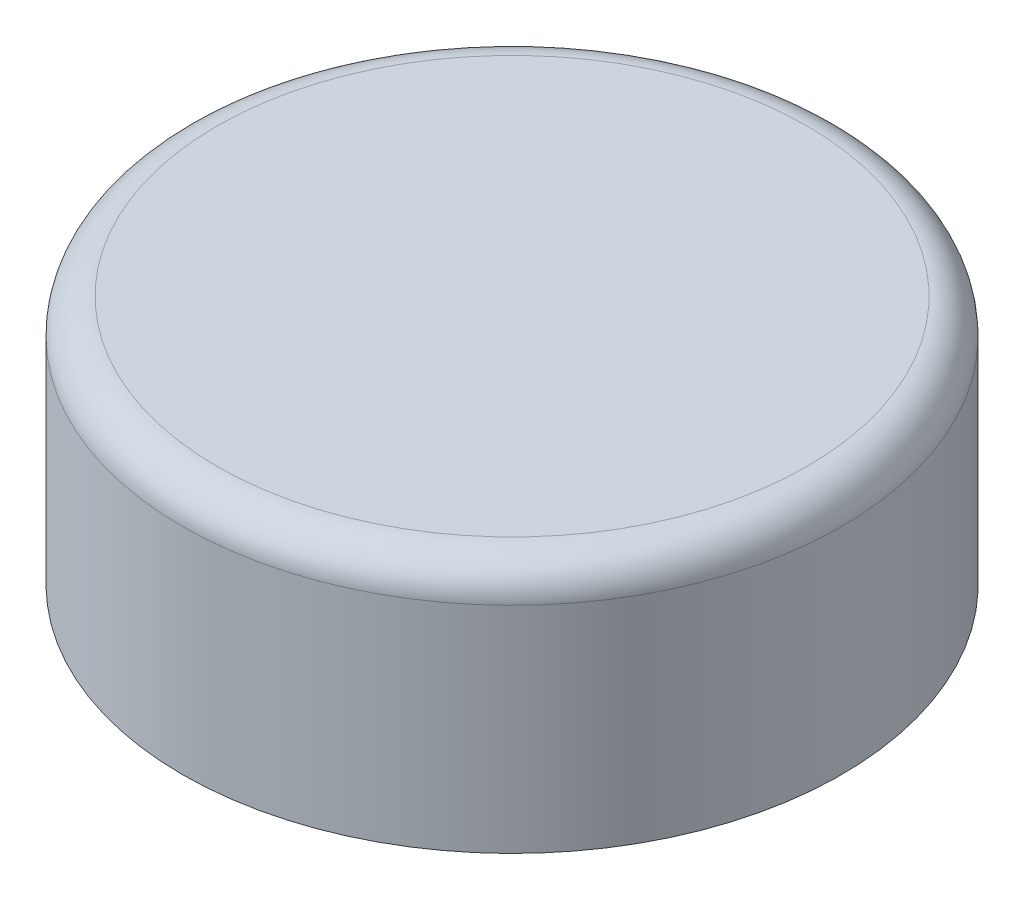
SolidWorks part; units mm, degrees
ref_plane "Front XY" through (0, 0, 0) normal (0, 0, 1) x (1, 0, 0)
ref_plane "Top XZ" through (0, 0, 0) normal (0, 1, 0) x (1, 0, 0)
ref_plane "Right YZ" through (0, 0, 0) normal (1, 0, 0) x (0, 0, -1)
sketch "Sketch1" plane through (0, 0, 0) normal (0, 1, 0) x (1, 0, 0)
  circle A0 centre (0, 0) radius 30.188
extrude "Extrude1" add sketch "Sketch1" along normal blind 22.86
fillet "Fillet2" radius 3.175 1 edges at (0, 22.86, 30.188)
sketch "Sketch3" plane through (0, 22.86, 0) normal (0, 1, 0) x (1, 0, 0)
  circle A0 centre (0, 0) radius 30.188 construction
  circle A1 centre (0, 0) radius 30.188
  dimension "thickness" = 45.1835
